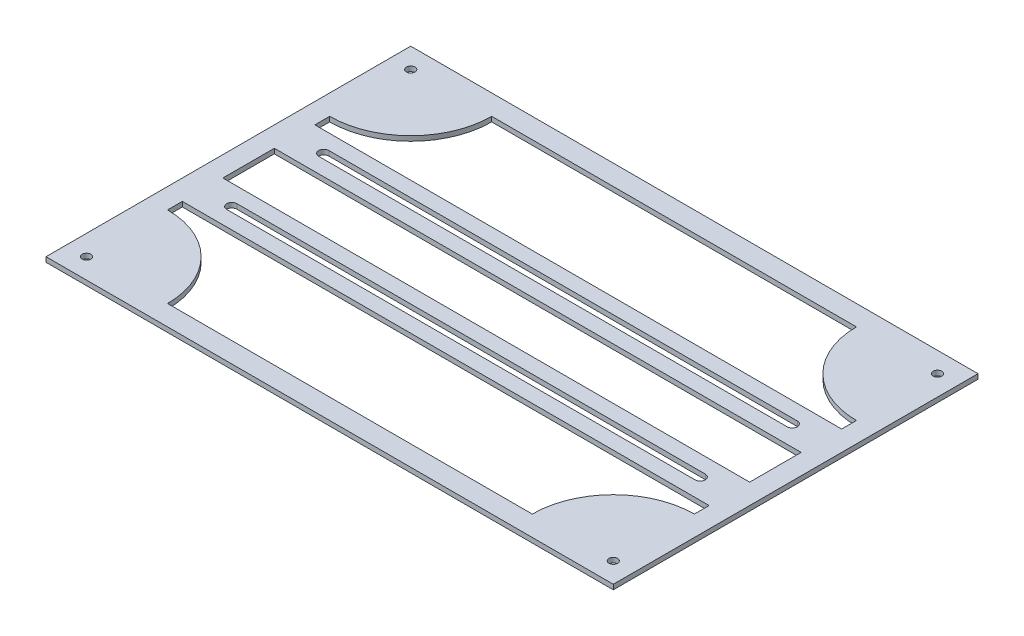
SolidWorks part; units mm, degrees
material "Acrylic (Medium-high impact)"
ref_plane "Front Plane" through (0, 0, 0) normal (0, 0, 1) x (1, 0, 0)
ref_plane "Top Plane" through (0, 0, 0) normal (0, 1, 0) x (1, 0, 0)
ref_plane "Right Plane" through (0, 0, 0) normal (1, 0, 0) x (0, 0, -1)
sketch "Sketch1" plane through (0, 0, 0) normal (0, 1, 0) x (1, 0, 0)
  line L0 (-82.55, -25.4) -> (-82.55, -20.7675)
  line L1 (88.9, -57.15) -> (-88.9, -57.15)
  line L2 (88.9, -57.15) -> (88.9, 57.15)
  line L3 (88.9, 57.15) -> (-88.9, 57.15)
  line L4 (-88.9, -57.15) -> (-88.9, 57.15)
  line L5 (88.9, -57.15) -> (-88.9, 57.15) construction
  line L6 (88.9, 57.15) -> (-88.9, -57.15) construction
  line L7 (57.15, -50.8) -> (-57.15, -50.8)
  line L8 (82.55, -25.4) -> (82.55, -20.7675)
  line L10 (82.55, -20.7675) -> (-82.55, -20.7675)
  line L11 (82.55, -8.0675) -> (-82.55, -8.0675)
  line L12 (0, 0) -> (-76.2, 0) construction
  line L13 (82.55, 8.0675) -> (-82.55, 8.0675)
  line L14 (82.55, 20.7675) -> (-82.55, 20.7675)
  line L15 (-82.55, -8.0675) -> (-82.55, 8.0675)
  line L16 (-82.55, -50.8) -> (-82.55, 50.8) construction
  line L17 (82.55, -8.0675) -> (82.55, 8.0675)
  line L18 (82.55, -50.8) -> (82.55, 50.8) construction
  line L19 (-82.55, 20.7675) -> (-82.55, 25.4)
  line L20 (82.55, 20.7675) -> (82.55, 25.4)
  line L21 (0, 0) -> (0, 34.6317) construction
  line L22 (82.55, 50.8) -> (-82.55, 50.8) construction
  line L23 (82.55, -50.8) -> (-82.55, -50.8) construction
  line L24 (57.15, 50.8) -> (-57.15, 50.8)
  arc A0 (-57.15, -50.8) -> (-82.55, -25.4) centre (-82.55, -50.8) ccw
  arc A1 (57.15, -50.8) -> (82.55, -25.4) centre (82.55, -50.8) cw
  arc A2 (57.15, 50.8) -> (82.55, 25.4) centre (82.55, 50.8) ccw
  arc A3 (-57.15, 50.8) -> (-82.55, 25.4) centre (-82.55, 50.8) cw
  point P0 (0, 0)
  dimension "D6" = 6.35
  dimension "D4" = 25.4
  dimension "D1" = 114.3
  dimension "D2" = 177.8
  dimension "D5" = 12.7
  dimension "D3" = 6.35
extrude "Boss-Extrude1" add sketch "Sketch1" along normal blind 1.524
sketch "Sketch3" plane through (0, 1.524, 0) normal (0, 1, 0) x (1, 0, 0)
  line L0 (-73.406, 14.4175) -> (73.406, 14.4175) construction
  line L1 (-73.406, 16.005) -> (73.406, 16.005)
  line L2 (-73.406, 12.83) -> (73.406, 12.83)
  line L3 (82.55, 20.7675) -> (-82.55, 20.7675) construction
  line L6 (82.55, 8.0675) -> (-82.55, 8.0675) construction
  line L7 (0, 0) -> (40.1052, 0) construction
  line L8 (-73.406, -14.4175) -> (73.406, -14.4175) construction
  line L9 (-73.406, -16.005) -> (73.406, -16.005)
  line L10 (-73.406, -12.83) -> (73.406, -12.83)
  arc A0 (-73.406, 16.005) -> (-73.406, 12.83) centre (-73.406, 14.4175) ccw
  arc A1 (73.406, 12.83) -> (73.406, 16.005) centre (73.406, 14.4175) ccw
  arc A2 (-73.406, -16.005) -> (-73.406, -12.83) centre (-73.406, -14.4175) cw
  arc A3 (73.406, -12.83) -> (73.406, -16.005) centre (73.406, -14.4175) cw
  point P2 (0, 14.4175)
  point P11 (0, 8.0675)
  point P17 (0, -14.4175)
  dimension "D1" = 1.5875
  dimension "D2" = 6.35
  dimension "D3" = 146.812
extrude "Cut-Extrude1" cut sketch "Sketch3" against normal through all
hole_wizard "#6-32 Tapped Hole1" positions "Sketch4" profile "Sketch5" tap size "#6-32" standard "Ansi Inch" end condition through all
sketch "Sketch4" plane through (0, 7.8105, 0) normal (0, 1, 0) x (-1, 0, 0)
  line L2 (0, 0) -> (0, 35.5851) construction
  line L4 (0, 0) -> (43.0458, 0) construction
  point P0 (82.55, -50.8)
  point P15 (82.55, 50.8)
  point P16 (-82.55, 50.8)
  point P17 (-82.55, -50.8)
sketch "Sketch5" plane through (-82.55, 7.8105, -50.8) normal (1, 0, 0) x (0, 0, 1)
  line L0 (0, 0) -> (0, 7.8105)
  line L1 (0, 7.8105) -> (1.3525, 7.8105)
  line L2 (1.3525, 7.8105) -> (1.3525, 0)
  line L3 (1.3525, 0) -> (0, 0)
  line L4 (0, -6.35) -> (0, 107.95) construction
  dimension "Thru Tap Drill Dia." = 2.7051
  dimension "Thru Tap Drill Depth" = 7.8105
cosmetic thread "Hole Thread1" parameters "D2"=3.5052
cosmetic thread "Hole Thread2" parameters "D2"=3.5052
cosmetic thread "Hole Thread9" parameters "D2"=3.5052
cosmetic thread "Hole Thread10" parameters "D2"=3.5052
hole_wizard "#6-32 Tapped Hole2" positions "Sketch6" profile "Sketch7" tap size "#6-32" standard "Ansi Inch" end condition through all
sketch "Sketch6" plane through (0, 1.524, 0) normal (0, 1, 0) x (-1, 0, 0)
  line L2 (0, 0) -> (0, 35.5851) construction
  line L4 (0, 0) -> (43.0458, 0) construction
  point P0 (82.55, -50.8)
  point P15 (82.55, 50.8)
  point P16 (-82.55, 50.8)
  point P17 (-82.55, -50.8)
sketch "Sketch7" plane through (-82.55, 1.524, -50.8) normal (1, 0, 0) x (0, 0, 1)
  line L0 (0, 0) -> (0, 1.524)
  line L1 (0, 1.524) -> (1.3525, 1.524)
  line L2 (1.3525, 1.524) -> (1.3525, 0)
  line L3 (1.3525, 0) -> (0, 0)
  line L4 (0, -6.35) -> (0, 107.95) construction
  dimension "Thru Tap Drill Dia." = 2.7051
  dimension "Thru Tap Drill Depth" = 1.524
equation "\"D2@Sketch3\" = \"D5@Sketch1\"/2"
